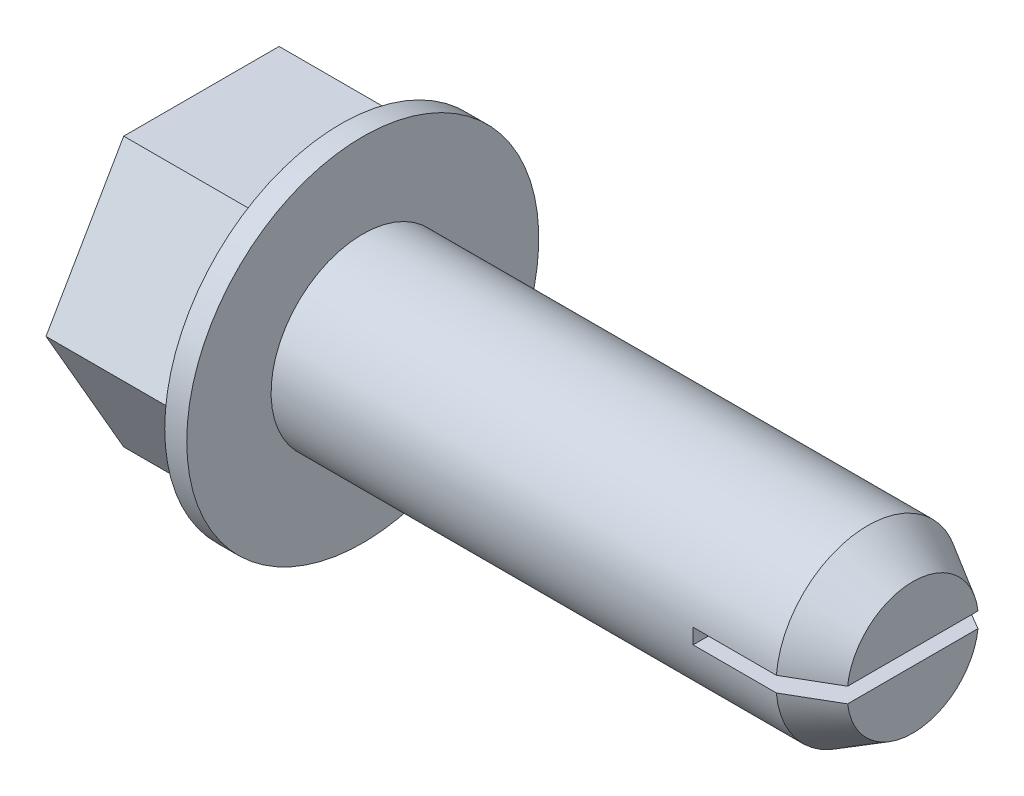
SolidWorks part; units mm, degrees
ref_plane "Front" through (0, 0, 0) normal (0, 0, 1) x (1, 0, 0)
ref_plane "Top" through (0, 0, 0) normal (0, 1, 0) x (1, 0, 0)
ref_plane "Right" through (0, 0, 0) normal (1, 0, 0) x (0, 0, -1)
ref_plane "Plane1" through (0, 0, 0) normal (0, 0, -1) x (-1, 0, 0)
sketch "Sketch1" plane through (0, 0, 0) normal (0, 0, -1) x (-1, 0, 0)
  line L0 (0, 6.096) -> (0, 0)
  line L1 (0, 0) -> (0.762, 0)
  line L2 (0.762, 0) -> (0.762, 6.096)
  line L3 (0.762, 6.096) -> (0, 6.096)
  line L4 (0, 0) -> (0.762, 0) construction
revolve "Revolve1" add sketch "Sketch1" angle 360 about L4
sketch "Sketch2" plane through (0, 0, 0) normal (1, 0, 0) x (0, 0, -1)
  circle A0 centre (0, 0) radius 3.175
extrude "Boss-Extrude1" add sketch "Sketch2" along normal blind 19.05
sketch "Sketch3" plane through (19.05, 0, 0) normal (1, 0, 0) x (0, 0, -1)
  line L0 (-3.164, -0.2646) -> (3.164, -0.2646)
  arc A0 (3.164, -0.2646) -> (-3.164, -0.2646) centre (0, 0) ccw
extrude "Cut-Extrude1" cut sketch "Sketch3" against normal blind 4.445
sketch "Sketch4" plane through (14.605, 0, 0) normal (1, 0, 0) x (0, 0, -1)
  line L0 (3.164, 0.2646) -> (-3.164, 0.2646)
  arc A0 (-3.164, 0.2646) -> (3.164, 0.2646) centre (0, 0) cw
extrude "Boss-Extrude2" add sketch "Sketch4" along normal blind 4.445
sketch "Sketch5" plane through (-0.762, 0, 0) normal (-1, 0, 0) x (0, 0, 1)
  line L0 (-2.691, -4.6609) -> (-5.3819, 0)
  line L1 (-5.3819, 0) -> (-2.691, 4.6609)
  line L2 (-2.691, 4.6609) -> (2.691, 4.6609)
  line L3 (2.691, 4.6609) -> (5.3819, 0)
  line L4 (5.3819, 0) -> (2.691, -4.6609)
  line L5 (2.691, -4.6609) -> (-2.691, -4.6609)
extrude "Boss-Extrude3" add sketch "Sketch5" along normal blind 4.826
hole_wizard "M6.5 Clearance Hole1" positions "Sketch7" profile "Sketch6" hole size "M6.5" standard "ANSI Metric"
sketch "Sketch7" plane through (-5.588, 0, 0) normal (-1, 0, 0) x (0, 0, 1)
  point P0 (0, 0)
sketch "Sketch6" plane through (-5.588, 0, 0) normal (0, 1, 0) x (0, 0, 1)
  line L0 (0, 0) -> (0, 0.9652)
  line L1 (0, 0.9652) -> (3.7287, 0.9652)
  line L2 (3.7287, 0.9652) -> (3.7287, 0)
  line L5 (3.7287, 0) -> (0, 0)
  line L10 (0, 0.9652) -> (-3.7287, 0.9652) construction
  line L11 (0, -6.35) -> (0, 107.95) construction
  dimension "Hole Dia." = 7.4574
  dimension "Hole Depth" = 0.9652
  dimension "Drill Angle" = 180
chamfer "Chamfer1" distance 0.9017 angle 60 2 edges at (19.05, 3.175, 0) (19.05, -3.175, 0)
